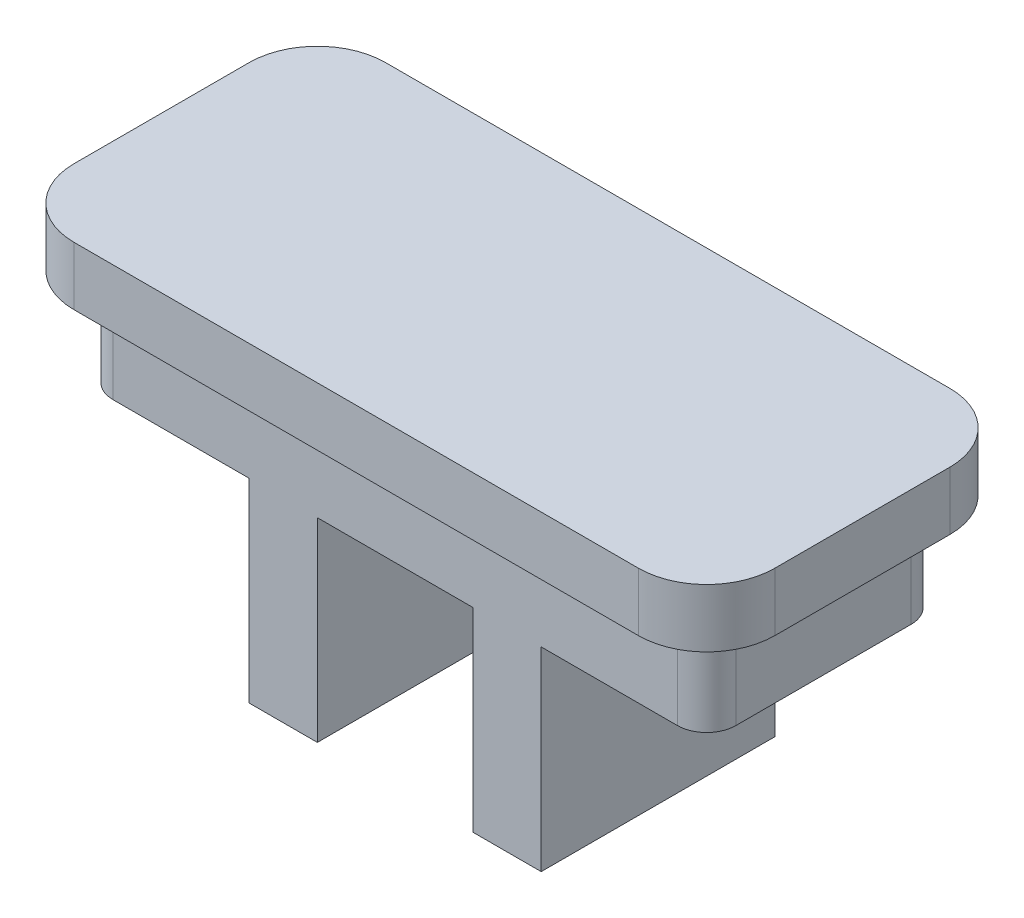
SolidWorks part; units mm, degrees
ref_plane "Front Plane" through (0, 0, 0) normal (0, 0, 1) x (1, 0, 0)
ref_plane "Top Plane" through (0, 0, 0) normal (0, 1, 0) x (1, 0, 0)
ref_plane "Right Plane" through (0, 0, 0) normal (1, 0, 0) x (0, 0, -1)
sketch "Sketch1" plane through (0, 0, 0) normal (0, 1, 0) x (1, 0, 0)
  line L1 (1.5, 0) -> (30.5, 0)
  line L2 (0, 1.5) -> (0, 10.5)
  line L3 (1.5, 12) -> (30.5, 12)
  line L4 (32, 1.5) -> (32, 10.5)
  arc A0 (30.5, 12) -> (32, 10.5) centre (30.5, 10.5) cw
  arc A1 (1.5, 0) -> (0, 1.5) centre (1.5, 1.5) cw
  arc A2 (30.5, 0) -> (32, 1.5) centre (30.5, 1.5) ccw
  arc A3 (0, 10.5) -> (1.5, 12) centre (1.5, 10.5) cw
  point P7 (32, 12)
  point P10 (0, 0)
  point P15 (0, 12)
  dimension "D3" = 1.5
  dimension "D1" = 32
  dimension "D2" = 12
extrude "Boss-Extrude1" add sketch "Sketch1" along normal blind 15
sketch "Sketch2" plane through (0, 15, 0) normal (0, 1, 0) x (1, 0, 0)
  line L4 (30.5, 12) -> (1.5, 12)
  line L5 (0, 10.5) -> (0, 1.5)
  line L6 (1.5, 0) -> (30.5, 0)
  line L7 (32, 1.5) -> (32, 10.5)
  line L8 (30.5, 12) -> (1.5, 12)
  line L9 (0, 10.5) -> (0, 1.5)
  line L10 (1.5, 0) -> (30.5, 0)
  line L11 (32, 1.5) -> (32, 10.5)
  line L16 (30.5, 14) -> (1.5, 14)
  line L17 (-2, 10.5) -> (-2, 1.5)
  line L18 (1.5, -2) -> (30.5, -2)
  line L19 (34, 1.5) -> (34, 10.5)
  line L20 (30.5, 14) -> (1.5, 14)
  line L21 (-2, 10.5) -> (-2, 1.5)
  line L22 (1.5, -2) -> (30.5, -2)
  line L23 (34, 1.5) -> (34, 10.5)
  arc A4 (32, 10.5) -> (30.5, 12) centre (30.5, 10.5) ccw
  arc A5 (1.5, 12) -> (0, 10.5) centre (1.5, 10.5) ccw
  arc A6 (0, 1.5) -> (1.5, 0) centre (1.5, 1.5) ccw
  arc A7 (30.5, 0) -> (32, 1.5) centre (30.5, 1.5) ccw
  arc A8 (32, 10.5) -> (30.5, 12) centre (30.5, 10.5) ccw
  arc A9 (1.5, 12) -> (0, 10.5) centre (1.5, 10.5) ccw
  arc A10 (0, 1.5) -> (1.5, 0) centre (1.5, 1.5) ccw
  arc A11 (30.5, 0) -> (32, 1.5) centre (30.5, 1.5) ccw
  arc A16 (34, 10.5) -> (30.5, 14) centre (30.5, 10.5) ccw
  arc A17 (1.5, 14) -> (-2, 10.5) centre (1.5, 10.5) ccw
  arc A18 (-2, 1.5) -> (1.5, -2) centre (1.5, 1.5) ccw
  arc A19 (30.5, -2) -> (34, 1.5) centre (30.5, 1.5) ccw
  arc A20 (34, 10.5) -> (30.5, 14) centre (30.5, 10.5) ccw
  arc A21 (1.5, 14) -> (-2, 10.5) centre (1.5, 10.5) ccw
  arc A22 (-2, 1.5) -> (1.5, -2) centre (1.5, 1.5) ccw
  arc A23 (30.5, -2) -> (34, 1.5) centre (30.5, 1.5) ccw
  arc M17 (32, 10.5) -> (30.5, 12) centre (30.5, 10.5) ccw
  line M18 (30.5, 12) -> (1.5, 12)
  arc M19 (1.5, 12) -> (0, 10.5) centre (1.5, 10.5) ccw
  line M20 (0, 10.5) -> (0, 1.5)
  arc M21 (0, 1.5) -> (1.5, 0) centre (1.5, 1.5) ccw
  line M22 (1.5, 0) -> (30.5, 0)
  arc M23 (30.5, 0) -> (32, 1.5) centre (30.5, 1.5) ccw
  line M24 (32, 1.5) -> (32, 10.5)
  dimension "D1" = 0
  dimension "D2" = 2
extrude "Boss-Extrude2" add sketch "Sketch2" along normal blind 3 contours M24 M17 M18 M19 M20 M21 M22 M23 | L22 A23 L23 A20 L20 A21 L21 A22 M17 M24 M23 M22 M21 M20 M19 M18
sketch "Sketch3" plane through (0, 0, 0) normal (0, -1, 0) x (1, 0, 0)
  line L0 (30.5, -12) -> (1.5, -12) construction
  line L1 (32, -1.5) -> (32, -10.5) construction
  line L3 (20, 0) -> (12, 0)
  line L4 (20, 0) -> (20, -12)
  line L5 (20, -12) -> (12, -12)
  line L6 (12, 0) -> (12, -12)
  line L7 (20, 0) -> (12, -12) construction
  line L8 (20, -12) -> (12, 0) construction
  point P0 (16, -12)
  point P1 (32, -6)
  point P4 (16, -6)
  point P7 (16, -6)
  dimension "D1" = 8
extrude "Cut-Extrude1" cut sketch "Sketch3" against normal blind 10
sketch "Sketch4" plane through (0, 0, 0) normal (0, -1, 0) x (1, 0, 0)
  line L1 (12, 0) -> (1.5, 0) construction
  line L2 (0, -1.5) -> (0, -10.5) construction
  line L3 (1.5, -12) -> (12, -12) construction
  line L5 (20, -12) -> (30.5, -12) construction
  line L6 (32, -10.5) -> (32, -1.5) construction
  line L7 (30.5, 0) -> (20, 0) construction
  line L9 (8.5, 0) -> (1.5, 0)
  line L10 (0, -1.5) -> (0, -10.5)
  line L11 (1.5, -12) -> (8.5, -12)
  line L13 (23.5, -12) -> (30.5, -12)
  line L14 (32, -10.5) -> (32, -1.5)
  line L15 (30.5, 0) -> (23.5, 0)
  line L16 (23.5, -12) -> (23.5, 0)
  line L17 (8.5, -12) -> (8.5, 0)
  arc A0 (1.5, 0) -> (0, -1.5) centre (1.5, -1.5) ccw construction
  arc A1 (0, -10.5) -> (1.5, -12) centre (1.5, -10.5) ccw construction
  arc A2 (30.5, -12) -> (32, -10.5) centre (30.5, -10.5) ccw construction
  arc A3 (32, -1.5) -> (30.5, 0) centre (30.5, -1.5) ccw construction
  arc A4 (1.5, 0) -> (0, -1.5) centre (1.5, -1.5) ccw
  arc A5 (0, -10.5) -> (1.5, -12) centre (1.5, -10.5) ccw
  arc A6 (30.5, -12) -> (32, -10.5) centre (30.5, -10.5) ccw
  arc A7 (32, -1.5) -> (30.5, 0) centre (30.5, -1.5) ccw
  dimension "D1" = 7
  dimension "D2" = 7
extrude "Cut-Extrude3" cut sketch "Sketch4" against normal blind 10
